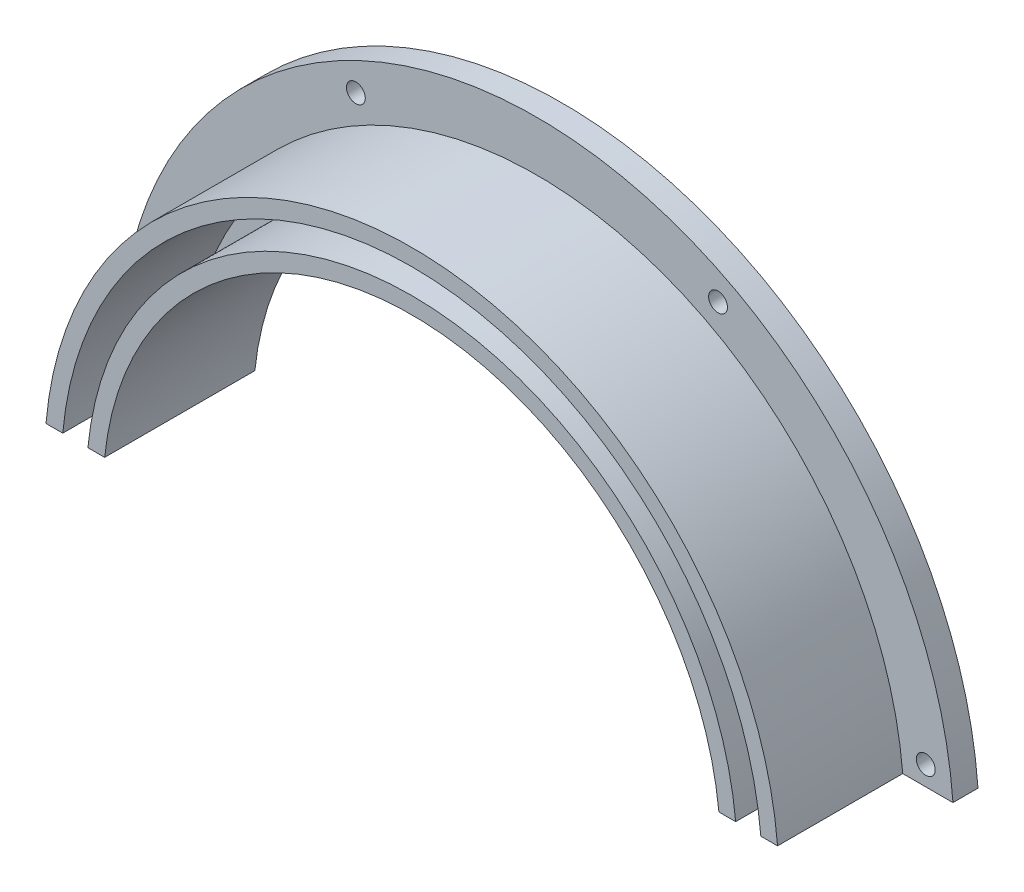
SolidWorks part; units mm, degrees
material "6061-T6 (SS)"
ref_plane "Front Plane" through (0, 0, 0) normal (0, 0, 1) x (1, 0, 0)
ref_plane "Top Plane" through (0, 0, 0) normal (0, 1, 0) x (1, 0, 0)
ref_plane "Right Plane" through (0, 0, 0) normal (1, 0, 0) x (0, 0, -1)
sketch "Sketch1" plane through (0, 0, 0) normal (1, 0, 0) x (0, 0, -1)
  line L0 (0, 0) -> (-52.3039, 0) construction
  line L1 (0, 37) -> (-18, 37)
  line L2 (-18, 37) -> (-18, 39)
  line L3 (-18, 39) -> (-3, 39)
  line L4 (-3, 39) -> (-3, 42)
  line L5 (-3, 42) -> (-18, 42)
  line L6 (-18, 42) -> (-18, 44)
  line L7 (-18, 44) -> (-3, 44)
  line L8 (-3, 44) -> (-3, 50)
  line L9 (-3, 50) -> (0, 50)
  line L10 (0, 50) -> (0, 37)
  dimension "D1" = 2
  dimension "D2" = 3
  dimension "D3" = 2
  dimension "D4" = 3
  dimension "D5" = 39
  dimension "D6" = 18
  dimension "D7" = 6
revolve "Revolve1" add sketch "Sketch1" angle 180 mid plane about L0
sketch "Sketch2" plane through (0, 0, 0) normal (0, 0, -1) x (-1, 0, 0)
  line L1 (-81.0365, 3.8) -> (81.0365, 3.8)
  line L2 (-81.0365, 3.8) -> (-81.0365, 0)
  line L3 (-81.0365, 0) -> (81.0365, 0)
  line L4 (81.0365, 3.8) -> (81.0365, 0)
  point P4 (0, 0)
  dimension "D1" = 3.8
extrude "Cut-Extrude1" cut sketch "Sketch2" against normal through all
hole_wizard "#4-40 Tapped Hole1" positions "Sketch4" profile "Sketch3" tap size "#4-40" standard "ANSI Inch" end condition through all
sketch "Sketch4" plane through (0, 0, 0) normal (0, 0, -1) x (-1, 0, 0)
  line L0 (0, 0) -> (-18.7278, 0) construction
  line L1 (0, 0) -> (-26.0448, 3.4289) construction
  point P0 (-46.5979, 6.1347)
  dimension "D1" = 7.5
  dimension "D2" = 47
sketch "Sketch3" plane through (46.5979, 6.1347, 0) normal (1, 0, 0) x (0, 1, 0)
  line L0 (0, 0) -> (0, 18)
  line L1 (0, 18) -> (1.1303, 18)
  line L2 (1.1303, 18) -> (1.1303, 0.9271)
  line L3 (1.1303, 0.9271) -> (2.0574, 0)
  line L5 (2.0574, 0) -> (0, 0)
  line L6 (-1.1303, 0.9271) -> (-2.0574, 0) construction
  line L11 (0, -6.35) -> (0, 107.95) construction
  dimension "Thru Tap Drill Dia." = 2.2606
  dimension "Thru Tap Drill Depth" = 18
  dimension "Near C'Sink Dia." = 4.1148
  dimension "Near C'Sink Angle" = 90
cosmetic thread "Hole Thread1" parameters "D2"=2.8448
pattern_circular "CirPattern1" count 4 every 55 about axis through (0, 0, 0) along (0, 0, 1) of "#4-40 Tapped Hole1"
